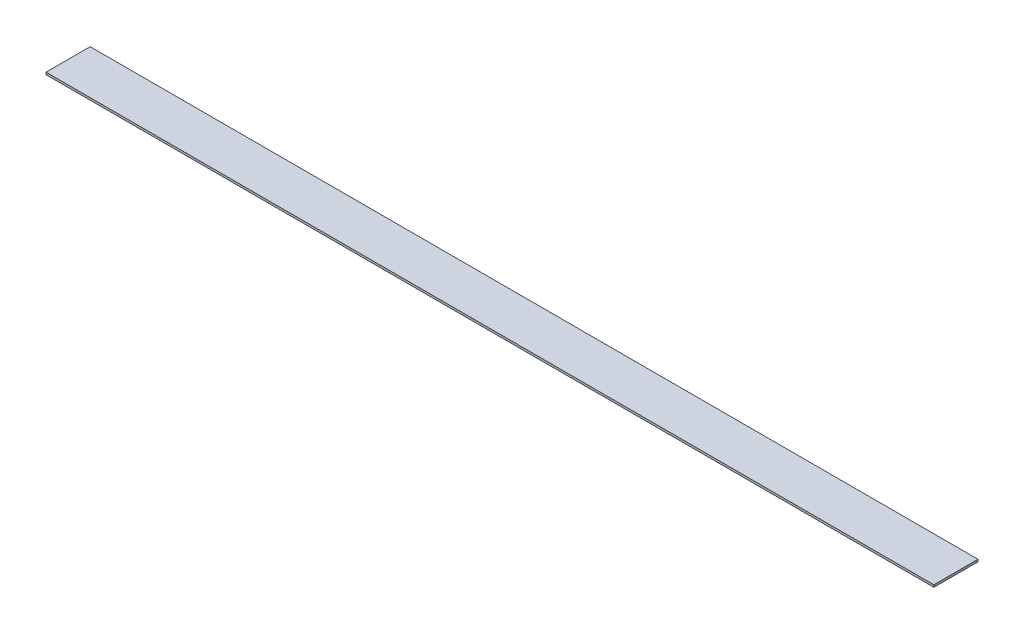
SolidWorks part; units mm, degrees
ref_plane "Front Plane" through (0, 0, 0) normal (0, 0, 1) x (1, 0, 0)
ref_plane "Top Plane" through (0, 0, 0) normal (0, 1, 0) x (1, 0, 0)
ref_plane "Right Plane" through (0, 0, 0) normal (1, 0, 0) x (0, 0, -1)
sketch "Sketch1" plane through (0, 0, 0) normal (0, 1, 0) x (1, 0, 0)
  line L1 (0, 0) -> (201.2, 0)
  line L2 (0, 0) -> (0, 10)
  line L3 (0, 10) -> (201.2, 10)
  line L4 (201.2, 0) -> (201.2, 10)
  dimension "D1" = 201.2
  dimension "D2" = 10
extrude "Boss-Extrude1" add sketch "Sketch1" along normal blind 0.5
